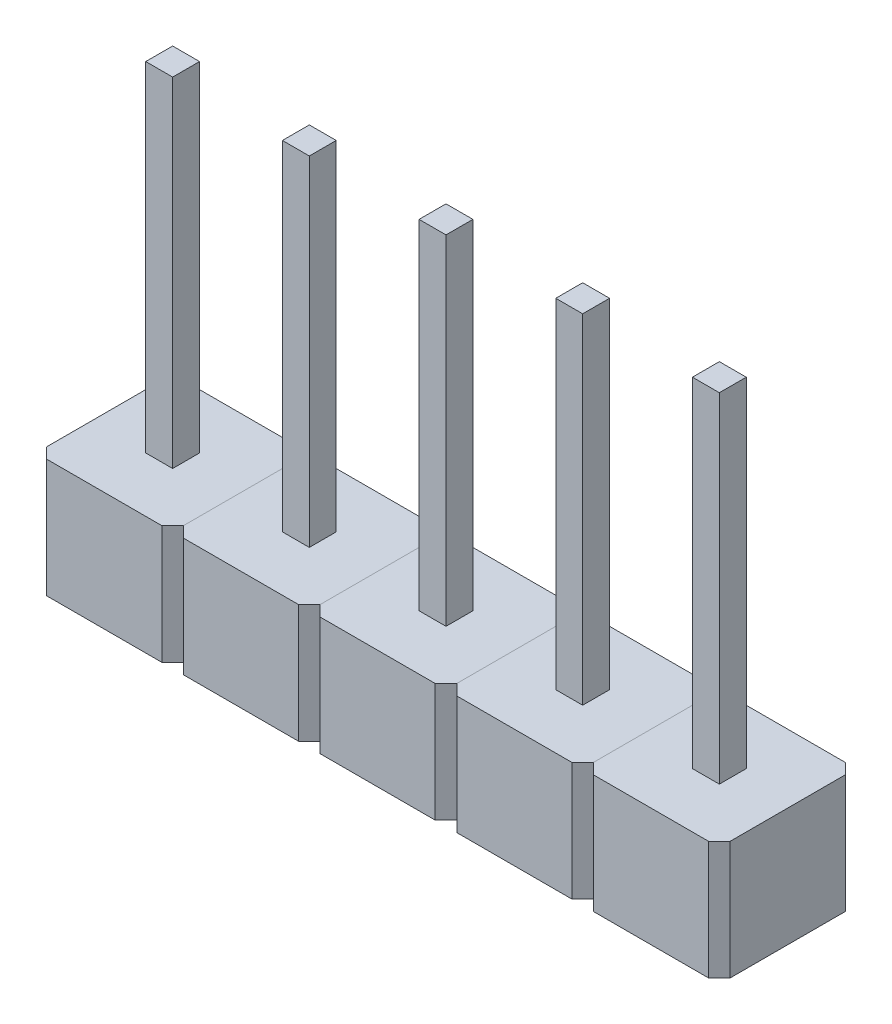
SolidWorks part; units mm, degrees
ref_plane "Alzado" through (0, 0, 0) normal (0, 0, 1) x (1, 0, 0)
ref_plane "Planta" through (0, 0, 0) normal (0, 1, 0) x (1, 0, 0)
ref_plane "Vista lateral" through (0, 0, 0) normal (1, 0, 0) x (0, 0, -1)
sketch "Croquis1" plane through (0, 0, 0) normal (0, 1, 0) x (1, 0, 0)
  line L0 (2.54, 0) -> (3.04, 0)
  line L1 (0, 0) -> (0.5, 0)
  line L2 (0, 0) -> (0, 0.5)
  line L3 (0, 0.5) -> (0.5, 0.5)
  line L4 (0.5, 0) -> (0.5, 0.5)
  line L5 (2.54, 0) -> (2.54, 0.5)
  line L6 (2.54, 0.5) -> (3.04, 0.5)
  line L7 (3.04, 0) -> (3.04, 0.5)
  line L8 (5.08, 0) -> (5.58, 0)
  line L9 (5.08, 0) -> (5.08, 0.5)
  line L10 (5.08, 0.5) -> (5.58, 0.5)
  line L11 (5.58, 0) -> (5.58, 0.5)
  line L12 (7.62, 0) -> (8.12, 0)
  line L13 (7.62, 0) -> (7.62, 0.5)
  line L14 (7.62, 0.5) -> (8.12, 0.5)
  line L15 (8.12, 0) -> (8.12, 0.5)
  line L16 (10.16, 0) -> (10.66, 0)
  line L17 (10.16, 0) -> (10.16, 0.5)
  line L18 (10.16, 0.5) -> (10.66, 0.5)
  line L19 (10.66, 0) -> (10.66, 0.5)
  dimension "D1" = 0.5
  dimension "D2" = 0.5
extrude "Extruir1" add sketch "Croquis1" along normal blind 8.5
sketch "Croquis2" plane through (0, 0, 0) normal (0, -1, 0) x (1, 0, 0)
  line L0 (0, 0) -> (0.5, 0) construction
  line L1 (-1.02, 1.02) -> (1.52, 1.02)
  line L2 (-1.02, 1.02) -> (-1.02, -1.52)
  line L3 (-1.02, -1.52) -> (1.52, -1.52)
  line L4 (1.52, 1.02) -> (1.52, -1.52)
  line L5 (0, -0.5) -> (0, 0) construction
  line L7 (0, 0) -> (0.5, 0)
  line L8 (0, 0) -> (0, -0.5)
  line L9 (0, -0.5) -> (0.5, -0.5)
  line L10 (0.5, 0) -> (0.5, -0.5)
  point P4 (0.25, 0)
  point P7 (0, -0.25)
  dimension "D1" = 2.54
  dimension "D2" = 2.54
  dimension "D3" = 1.27
  dimension "D4" = 1.27
extrude "Extruir2" add sketch "Croquis2" against normal blind 2.2 separate body
chamfer "Chaflán1" distance 0.2 angle 45 4 edges at (1.52, 1.1, -1.52) (1.52, 1.1, 1.02) (-1.02, 1.1, -1.52) (-1.02, 1.1, 1.02)
pattern_linear "MatrizL1" count 5 spacing 2.54 along (1, 0, 0) of bodies 106
